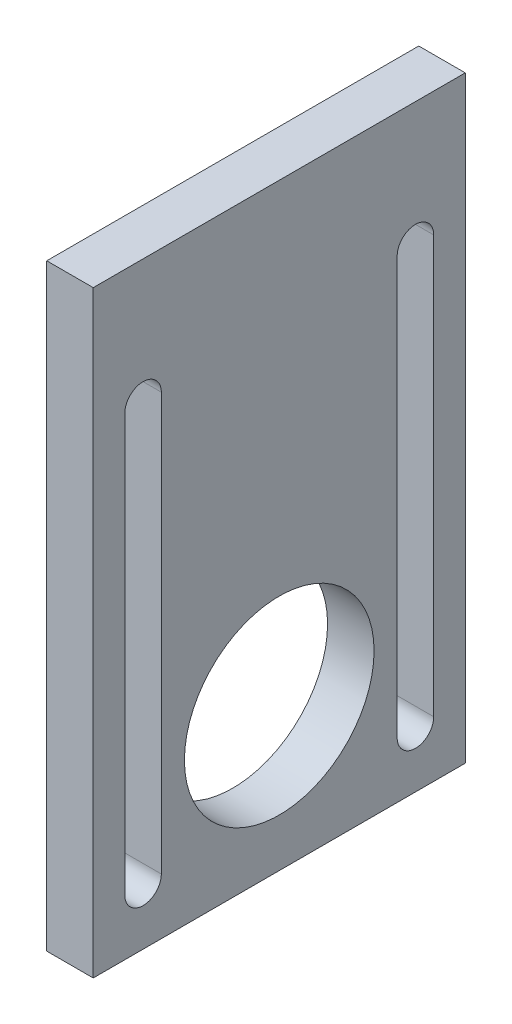
SolidWorks part; units mm, degrees
ref_plane "Front Plane" through (0, 0, 0) normal (0, 0, 1) x (1, 0, 0)
ref_plane "Top Plane" through (0, 0, 0) normal (0, 1, 0) x (1, 0, 0)
ref_plane "Right Plane" through (0, 0, 0) normal (1, 0, 0) x (0, 0, -1)
sketch "Sketch1" plane through (0, 0, 0) normal (1, 0, 0) x (0, 0, -1)
  line L1 (0, 0) -> (56, 0)
  line L2 (0, 0) -> (0, 90)
  line L3 (0, 90) -> (56, 90)
  line L4 (56, 0) -> (56, 90)
  dimension "D1" = 56
  dimension "D2" = 90
extrude "Boss-Extrude1" add sketch "Sketch1" along normal blind 7
sketch "Sketch2" plane through (7, 0, 0) normal (1, 0, 0) x (0, 0, -1)
  line L0 (0, 0) -> (56, 0) construction
  line L1 (28, 0) -> (28, 90) construction
  line L2 (56, 90) -> (0, 90) construction
  circle A0 centre (28, 21.5163) radius 14.275
  point P5 (28, 0)
  dimension "D1" = 28.55
extrude "Cut-Extrude1" cut sketch "Sketch2" against normal through all
sketch "Sketch3" plane through (7, 0, 0) normal (1, 0, 0) x (0, 0, -1)
  line L0 (7.5, 71.2448) -> (7.5, 8.435) construction
  line L1 (10.25, 71.2448) -> (10.25, 8.435)
  line L2 (4.75, 71.2448) -> (4.75, 8.435)
  line L3 (48.5, 8.435) -> (48.5, 71.2448) construction
  line L4 (45.75, 8.435) -> (45.75, 71.2448)
  line L5 (51.25, 8.435) -> (51.25, 71.2448)
  line L6 (0, 90) -> (0, 0) construction
  line L7 (56, 0) -> (56, 90) construction
  arc A0 (10.25, 71.2448) -> (4.75, 71.2448) centre (7.5, 71.2448) ccw
  arc A1 (4.75, 8.435) -> (10.25, 8.435) centre (7.5, 8.435) ccw
  arc A2 (45.75, 8.435) -> (51.25, 8.435) centre (48.5, 8.435) ccw
  arc A3 (51.25, 71.2448) -> (45.75, 71.2448) centre (48.5, 71.2448) ccw
  point P2 (7.5, 39.8399)
  point P7 (48.5, 39.8399)
  dimension "D1" = 2.75
  dimension "D2" = 2.75
  dimension "D3" = 7.5
  dimension "D4" = 7.5
extrude "Cut-Extrude2" cut sketch "Sketch3" against normal through all
